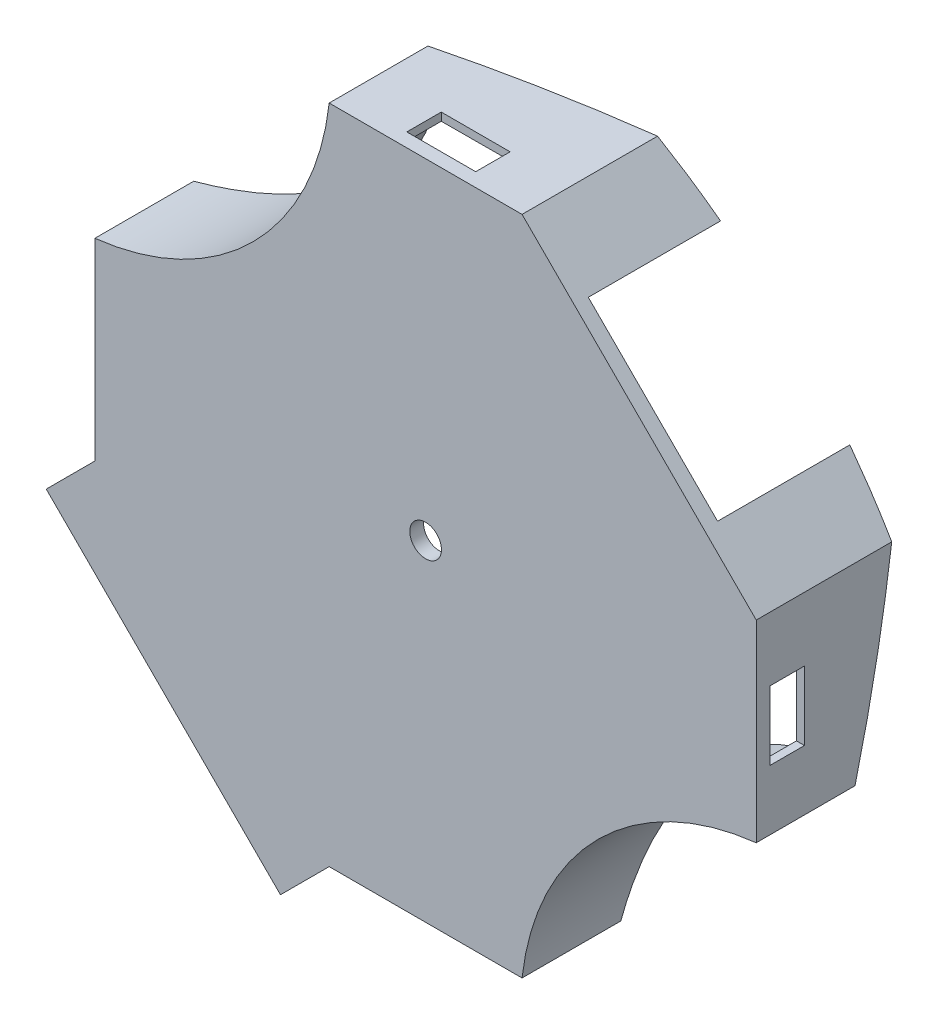
SolidWorks part; units mm, degrees
ref_plane "Front Plane" through (0, 0, 0) normal (0, 0, 1) x (1, 0, 0)
ref_plane "Top Plane" through (0, 0, 0) normal (0, 1, 0) x (1, 0, 0)
ref_plane "Right Plane" through (0, 0, 0) normal (1, 0, 0) x (0, 0, -1)
sketch "Sketch1" plane through (0, 0, 0) normal (0, 0, 1) x (1, 0, 0)
  line L0 (-84.4424, 11.0837) -> (-50.4424, -22.9163) construction
  line L1 (-50.4424, -22.9163) -> (-22.4424, -22.9163)
  line L2 (-84.4424, 39.0837) -> (-84.4424, 11.0837)
  line L3 (-50.4424, 73.0837) -> (-22.4424, 73.0837)
  line L4 (-22.4424, 73.0837) -> (11.5576, 39.0837)
  line L5 (11.5576, 39.0837) -> (11.5576, 11.0837)
  line L6 (11.5576, 11.0837) -> (-84.4424, 11.0837) construction
  line L7 (-84.4424, 39.0837) -> (11.5576, 39.0837) construction
  line L8 (-50.4424, 73.0837) -> (-50.4424, 39.0837) construction
  line L9 (-50.4424, 39.0837) -> (-50.4424, 11.0837) construction
  line L10 (-50.4424, 11.0837) -> (-50.4424, -22.9163) construction
  line L11 (-22.4424, -22.9163) -> (-22.4424, 11.0837) construction
  line L12 (-22.4424, 11.0837) -> (-22.4424, 39.0837) construction
  line L13 (-22.4424, 39.0837) -> (-22.4424, 73.0837) construction
  line L14 (-84.4424, 11.0837) -> (-91.5134, 4.0126)
  line L17 (-91.5134, 4.0126) -> (-50.4424, -22.9163) construction
  line L18 (-84.4424, 25.0837) -> (-50.4424, 25.0837) construction
  line L19 (-91.5134, 4.0126) -> (-57.5134, -29.9874)
  line L20 (-57.5134, -29.9874) -> (-50.4424, -22.9163)
  line L21 (-50.4424, 25.0837) -> (-22.4424, 25.0837) construction
  line L22 (-22.4424, 25.0837) -> (11.5576, 25.0837) construction
  line L23 (-36.4424, 73.0837) -> (-36.4424, 39.0837) construction
  line L24 (-36.4424, 39.0837) -> (-36.4424, 11.0837) construction
  line L25 (-36.4424, 11.0837) -> (-36.4424, -22.9163) construction
  arc A2 (-84.4424, 39.0837) -> (-50.4424, 73.0837) centre (-88.6843, 77.3256) ccw
  arc A3 (-22.4424, -22.9163) -> (11.5576, 11.0837) centre (15.7678, -27.1264) cw
  circle A4 centre (-36.4424, 25.0837) radius 2.2992
  dimension "D1" = 28
  dimension "D3" = 38.4413
  dimension "D4" = 38.4765
  dimension "D2" = 48.0833
  dimension "D5" = 10
extrude "Boss-Extrude1" add sketch "Sketch1" along normal blind 2
sketch "Sketch2" plane through (0, 0, 2) normal (0, 0, 1) x (1, 0, 0)
  line L0 (-84.4424, 11.0837) -> (-84.4424, 39.0837) construction
  line L1 (-57.5134, -29.9874) -> (-50.4424, -22.9163) construction
  line L2 (-50.4424, -22.9163) -> (-22.4424, -22.9163) construction
  line L3 (11.5576, 11.0837) -> (11.5576, 39.0837)
  line L4 (11.5576, 39.0837) -> (3.9415, 46.6998)
  line L5 (-22.4424, 73.0837) -> (-50.4424, 73.0837)
  line L6 (-74.5134, -12.9874) -> (-5.4424, 56.0837) construction
  line L7 (-91.5134, 4.0126) -> (-57.5134, -29.9874) construction
  line L8 (-5.4424, 56.0837) -> (-6.2909, 55.2352) construction
  line L9 (-22.4424, 73.0837) -> (-22.9495, 71.9961) construction
  line L10 (11.5576, 39.0837) -> (10.4701, 38.5766) construction
  line L11 (11.5576, 11.0837) -> (10.3576, 11.0837) construction
  line L12 (-50.4424, 73.0837) -> (-50.4424, 71.8837) construction
  line L13 (-49.3946, 71.888) -> (-22.9495, 71.9961)
  line L14 (-22.9495, 71.9961) -> (-15.6236, 64.6702)
  line L15 (10.4701, 38.5766) -> (10.3619, 12.1315)
  line L16 (-61.4773, 50.1186) -> (-11.4144, 0.0557) construction
  line L17 (-84.4424, 39.0837) -> (-83.2424, 39.0837) construction
  line L18 (-22.4424, -22.9163) -> (-22.4424, -21.7163) construction
  line L19 (-50.4424, -22.9163) -> (-49.9352, -21.8287)
  line L20 (-84.4424, 11.0837) -> (-83.3548, 11.5908)
  line L21 (-67.4424, -5.9163) -> (-66.5938, -5.0678) construction
  line L22 (-49.9352, -21.8287) -> (-23.4901, -21.7206)
  line L23 (-83.3548, 11.5908) -> (-49.9352, -21.8287) construction
  line L24 (-83.2466, 38.0359) -> (-83.3548, 11.5908)
  line L25 (-84.4424, 11.0837) -> (-84.4424, 39.0837)
  line L26 (-50.4424, -22.9163) -> (-84.4424, 11.0837) construction
  line L27 (-22.4424, -22.9163) -> (-50.4424, -22.9163)
  line L28 (-83.2424, 39.2359) -> (-83.2429, 39.0837) construction
  line L29 (-50.5946, 71.8837) -> (-50.4424, 71.8842) construction
  line L30 (-61.4773, 50.1186) -> (-60.6288, 49.2701) construction
  line L34 (3.1442, 45.9025) -> (10.4701, 38.5766)
  line L35 (-14.8262, 65.4676) -> (-22.4424, 73.0837)
  line L36 (-14.8262, 65.4676) -> (-15.6236, 64.6702)
  line L38 (3.1442, 45.9025) -> (3.9415, 46.6998)
  arc A0 (-84.4424, 39.0837) -> (-50.4424, 73.0837) centre (-88.6843, 77.3256) ccw construction
  arc A1 (11.5576, 11.0837) -> (-22.4424, -22.9163) centre (15.7678, -27.1264) ccw construction
  arc A2 (-84.4424, 39.0837) -> (-50.4424, 73.0837) centre (-88.6843, 77.3256) ccw
  arc A3 (-83.2466, 38.0359) -> (-49.3946, 71.888) centre (-88.7223, 77.3636) ccw
  arc A4 (-23.4901, -21.7206) -> (10.3619, 12.1315) centre (15.8376, -27.1962) cw
  arc A5 (-22.4424, -22.9163) -> (11.5576, 11.0837) centre (15.7996, -27.1582) cw
  point P57 (-5.4424, 56.0837)
  point P62 (-4.5585, 55.1998)
  dimension "D1" = 1.2
  dimension "D2" = 65
  dimension "D3" = 65
  dimension "D4" = 1.2
  dimension "D5" = 1.2
  dimension "D6" = 1.2
extrude "Boss-Extrude2" add sketch "Sketch2" against normal blind 25
sketch "Sketch3" plane through (0, 0, 0) normal (0, 0, -1) x (-1, 0, 0)
  line L0 (36.4424, 25.0837) -> (36.7127, -21.7747) construction
  line L1 (49.9352, -21.8287) -> (23.4901, -21.7206) construction
  line L3 (31.7127, -21.7542) -> (31.7127, -22.9163)
  line L4 (50.4424, -22.9163) -> (22.4424, -22.9163) construction
  line L5 (31.7127, -22.9163) -> (41.7127, -22.9163)
  line L6 (41.7127, -22.9163) -> (41.7127, -21.7951)
  line L19 (31.7127, -21.7542) -> (31.7127, -21.5317)
  line L20 (31.7127, -21.5317) -> (41.7127, -21.5726)
  line L21 (41.7127, -21.5726) -> (41.7127, -21.7951)
  line L22 (-10.3956, 29.8134) -> (-11.5576, 29.8134)
  line L23 (-11.5576, 29.8134) -> (-11.5576, 19.8134)
  line L24 (-11.5576, 19.8134) -> (-10.4365, 19.8134)
  line L25 (-10.3956, 29.8134) -> (-10.1731, 29.8134)
  line L26 (-10.1731, 29.8134) -> (-10.214, 19.8134)
  line L27 (-10.214, 19.8134) -> (-10.4365, 19.8134)
  line L28 (41.172, 71.9216) -> (41.172, 73.0837)
  line L29 (41.172, 73.0837) -> (31.172, 73.0837)
  line L30 (31.172, 73.0837) -> (31.172, 71.9625)
  line L31 (41.172, 71.9216) -> (41.172, 71.6991)
  line L32 (41.172, 71.6991) -> (31.172, 71.74)
  line L33 (31.172, 71.74) -> (31.172, 71.9625)
  line L34 (83.2803, 20.354) -> (84.4424, 20.354)
  line L35 (84.4424, 20.354) -> (84.4424, 30.354)
  line L36 (84.4424, 30.354) -> (83.3212, 30.354)
  line L37 (83.2803, 20.354) -> (83.0578, 20.354)
  line L38 (83.0578, 20.354) -> (83.0987, 30.354)
  line L39 (83.0987, 30.354) -> (83.3212, 30.354)
  point P8 (36.7127, -21.7747)
  point P35 (36.4424, 25.0837)
  dimension "D2" = 10
  dimension "D1" = 4
extrude "Cut-Extrude1" cut sketch "Sketch3" along normal blind 5
sketch "Sketch4" plane through (25.3207, 25.3207, 0) normal (0.7071, 0.7071, 0) x (0.7071, -0.7071, 0)
  line L0 (-87.3461, 23) -> (-87.3461, 12.3355) construction
  line L1 (-87.3461, 12.3355) -> (0.3351, 12.3355) construction
  line L2 (0.3351, -2) -> (0.3351, 23) construction
  line L3 (0.3351, 12.3355) -> (0.3351, 23) construction
  line L4 (0.3351, 23) -> (-87.3461, 23) construction
  line L5 (-87.3461, 23) -> (-87.3461, 12.3355) construction
  line L6 (-67.5471, 23) -> (-67.5471, 12.3355) construction
  line L7 (-19.4639, 23) -> (-19.4639, 12.3355) construction
  line L8 (-19.4639, -2) -> (-19.4639, 23) construction
  line L9 (-87.3461, 12.3355) -> (-87.3461, 23)
  line L10 (-87.3461, 23) -> (0.3351, 23)
  line L11 (0.3351, 23) -> (0.3351, 12.3355)
  spline S0 degree 3 poles (-87.3461, 12.3355) (-59.4463, 22.3672) (-27.5647, 22.3672) (0.3351, 12.3355) knots 0 0 0 0 1 1 1 1
extrude "Cut-Extrude2" cut sketch "Sketch4" against normal through all
